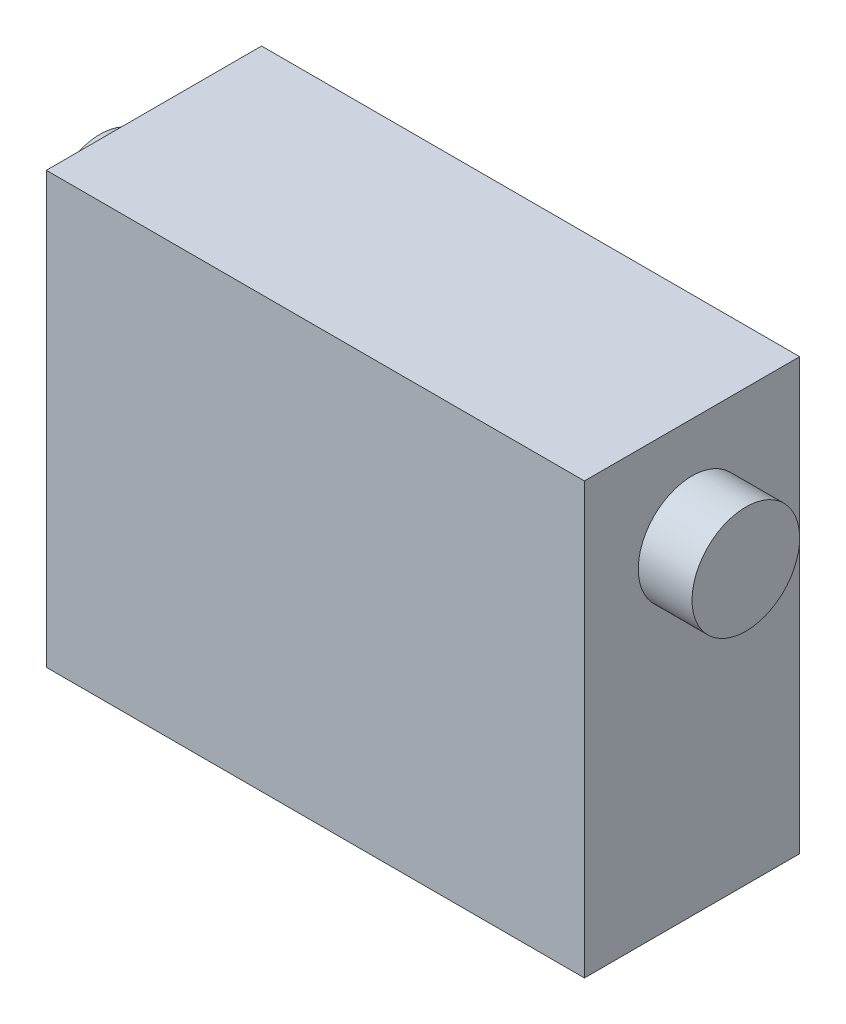
SolidWorks part; units mm, degrees
ref_plane "Front Plane" through (0, 0, 0) normal (0, 0, 1) x (1, 0, 0)
ref_plane "Top Plane" through (0, 0, 0) normal (0, 1, 0) x (1, 0, 0)
ref_plane "Right Plane" through (0, 0, 0) normal (1, 0, 0) x (0, 0, -1)
sketch "Sketch1" plane through (0, 0, 0) normal (0, 0, 1) x (1, 0, 0)
  line L1 (-25, 20) -> (25, 20)
  line L2 (-25, 20) -> (-25, -20)
  line L3 (-25, -20) -> (25, -20)
  line L4 (25, 20) -> (25, -20)
  line L5 (-25, 20) -> (25, -20) construction
  line L6 (-25, -20) -> (25, 20) construction
  point P0 (0, 0)
  dimension "D1" = 40
  dimension "D2" = 50
extrude "Boss-Extrude1" add sketch "Sketch1" along normal blind 20
sketch "Sketch2" plane through (-25, 0, 0) normal (-1, 0, 0) x (0, 0, 1)
  circle A0 centre (10, 10.4077) radius 5
  dimension "D1" = 10
extrude "Boss-Extrude2" add sketch "Sketch2" along normal blind 5 and the other way blind 55
